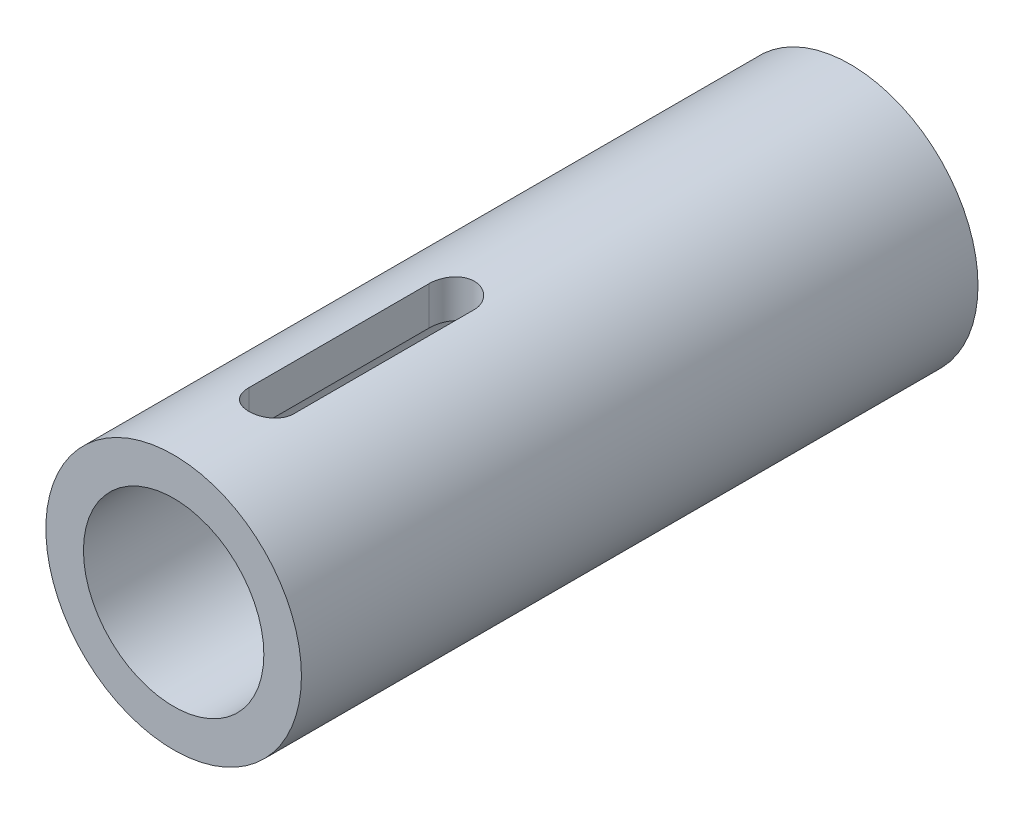
SolidWorks part; units mm, degrees
ref_plane "Front" through (0, 0, 0) normal (0, 0, 1) x (1, 0, 0)
ref_plane "Top" through (0, 0, 0) normal (0, 1, 0) x (1, 0, 0)
ref_plane "Right" through (0, 0, 0) normal (1, 0, 0) x (0, 0, -1)
sketch "Sketch1" plane through (0, 0, 0) normal (0, 0, 1) x (1, 0, 0)
  circle A0 centre (0, 0) radius 8.5
  circle A1 centre (0, 0) radius 6
  dimension "D1" = 17
  dimension "D2" = 12
extrude "Boss-Extrude1" add sketch "Sketch1" along normal blind 45
ref_plane "Plane1" through (0, 8.5, 0) normal (0, 1, 0) x (-1, 0, 0)
sketch "Sketch2" plane through (0, 8.5, 0) normal (0, 1, 0) x (-1, 0, 0)
  line L0 (0, 38.5) -> (0, 26.5) construction
  line L1 (1.5, 38.5) -> (1.5, 26.5)
  line L2 (-1.5, 38.5) -> (-1.5, 26.5)
  line L3 (6, 45) -> (-6, 45) construction
  arc A0 (1.5, 38.5) -> (-1.5, 38.5) centre (0, 38.5) ccw
  arc A1 (-1.5, 26.5) -> (1.5, 26.5) centre (0, 26.5) ccw
  point P2 (0, 32.5)
  dimension "D1" = 15
  dimension "D3" = 5
  dimension "D2" = 3
extrude "Cut-Extrude1" cut sketch "Sketch2" against normal up to next
